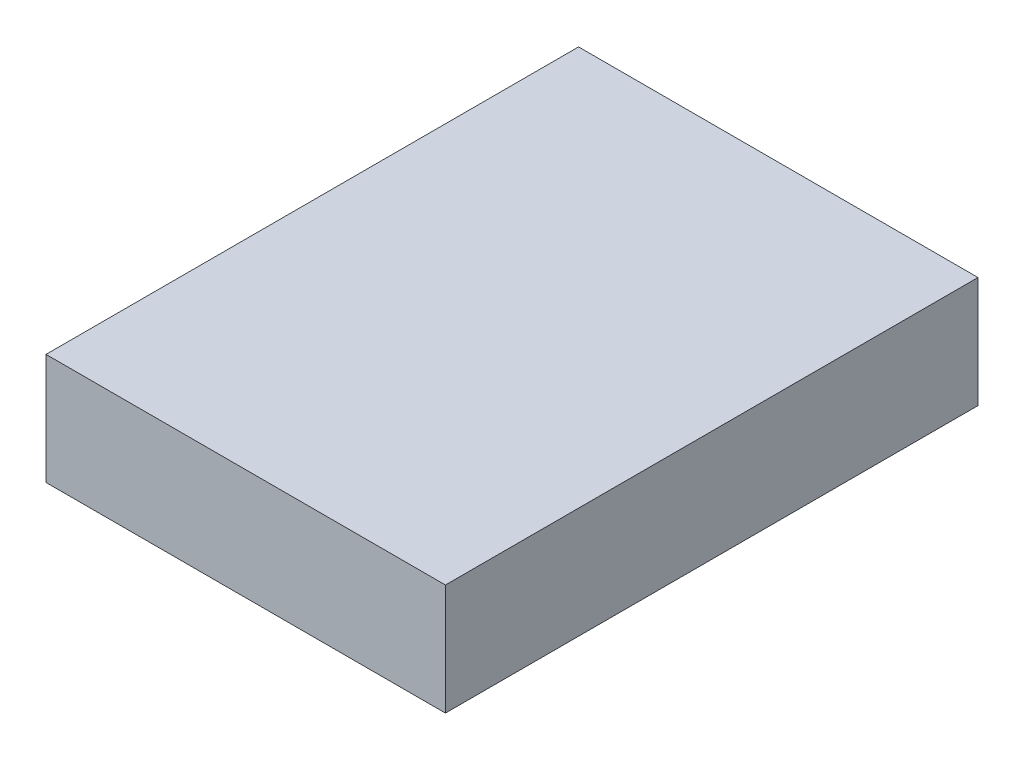
SolidWorks part; units mm, degrees
ref_plane "Front Plane" through (0, 0, 0) normal (0, 0, 1) x (1, 0, 0)
ref_plane "Top Plane" through (0, 0, 0) normal (0, 1, 0) x (1, 0, 0)
ref_plane "Right Plane" through (0, 0, 0) normal (1, 0, 0) x (0, 0, -1)
sketch "Sketch1" plane through (0, 0, 0) normal (0, 1, 0) x (1, 0, 0)
  line L1 (-9, 12) -> (9, 12)
  line L2 (-9, 12) -> (-9, -12)
  line L3 (-9, -12) -> (9, -12)
  line L4 (9, 12) -> (9, -12)
  line L5 (-9, 12) -> (9, -12) construction
  line L6 (-9, -12) -> (9, 12) construction
  point P0 (0, 0)
  dimension "D1" = 24
  dimension "D2" = 18
extrude "Boss-Extrude1" add sketch "Sketch1" along normal blind 5
